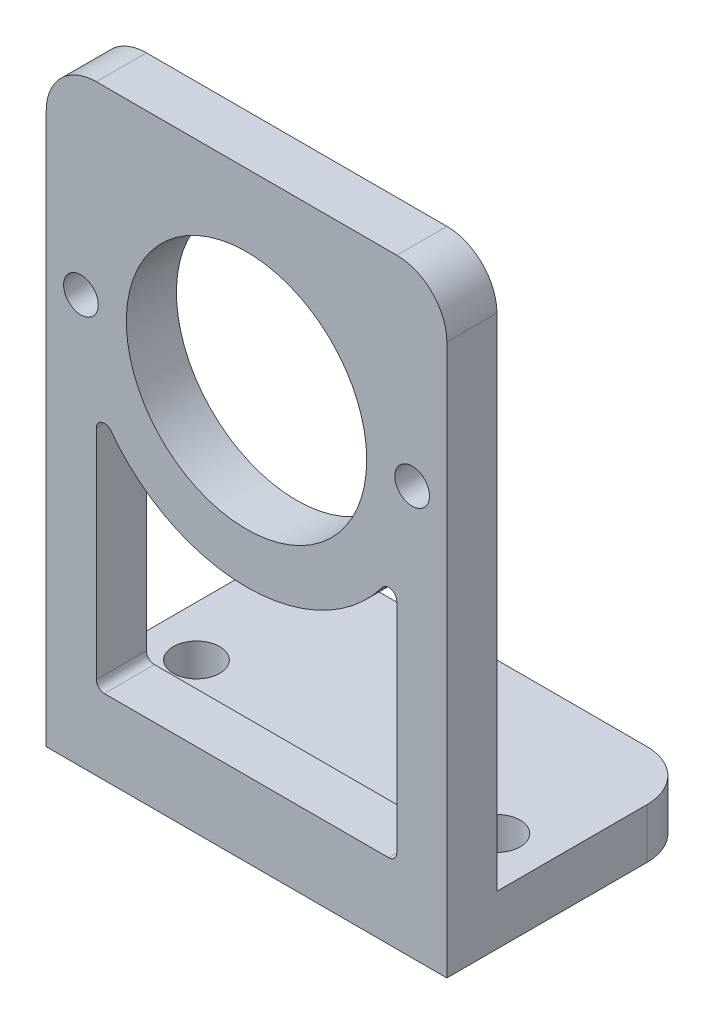
SolidWorks part; units mm, degrees
material "6061-T6 (SS)"
ref_plane "Front Plane" through (0, 0, 0) normal (0, 0, 1) x (1, 0, 0)
ref_plane "Top Plane" through (0, 0, 0) normal (0, 1, 0) x (1, 0, 0)
ref_plane "Right Plane" through (0, 0, 0) normal (1, 0, 0) x (0, 0, -1)
sketch "Sketch1" plane through (0, 0, 0) normal (1, 0, 0) x (0, 0, -1)
  line L0 (0, 38.1) -> (0, 0)
  line L1 (0, 0) -> (15.875, 0)
  line L2 (15.875, 0) -> (15.875, 3.175)
  line L3 (15.875, 3.175) -> (3.175, 3.175)
  line L4 (3.175, 3.175) -> (3.175, 38.1)
  line L5 (3.175, 38.1) -> (0, 38.1)
  dimension "D1" = 38.1
  dimension "D2" = 12.7
  dimension "D3" = 3.175
extrude "Boss-Extrude1" add sketch "Sketch1" along normal mid plane 25.4
sketch "Sketch2" plane through (0, 0, 0) normal (0, 0, 1) x (1, 0, 0)
  line L0 (12.7, 0) -> (-12.7, 0) construction
  circle A0 centre (0, 25.908) radius 7.62
  dimension "D2" = 15.24
  dimension "D1" = 25.908
extrude "Cut-Extrude1" cut sketch "Sketch2" against normal through all
fillet "Fillet1" radius 3.175 4 edges at (-12.7, 1.5875, -15.875) (12.7, 1.5875, -15.875) (-12.7, 38.1, -1.5875) (12.7, 38.1, -1.5875)
hole_wizard "#4 Clearance Hole1" positions "Sketch3" profile "Sketch4" hole size "#4" standard "ANSI Inch" end condition through all
sketch "Sketch3" plane through (0, 3.175, 0) normal (0, 1, 0) x (1, 0, 0)
  line L0 (-9.525, 6.35) -> (0, 0)
  line L1 (0, 0) -> (9.525, 6.35)
  line L3 (12.7, 3.175) -> (-12.7, 3.175) construction
  point P0 (-9.525, 6.35)
  point P2 (0, 12.7)
  point P4 (9.525, 6.35)
  dimension "D1" = 19.05
  dimension "D2" = 6.35
  dimension "D3" = 3.175
sketch "Sketch4" plane through (-9.525, 3.175, -6.35) normal (1, 0, 0) x (0, 0, 1)
  line L0 (0, 0) -> (0, 3.175)
  line L1 (0, 3.175) -> (1.4732, 3.175)
  line L2 (1.4732, 3.175) -> (1.4732, 0)
  line L5 (1.4732, 0) -> (0, 0)
  line L11 (0, -6.35) -> (0, 107.95) construction
  dimension "Thru Hole Dia." = 2.9464
  dimension "Thru Hole Depth" = 3.175
hole_wizard "M2 Clearance Hole1" positions "Sketch5" profile "Sketch6" hole size "M2" standard "ANSI Metric" end condition through all
sketch "Sketch5" plane through (32.8513, 6.6459, 0) normal (0, 0, 1) x (0, 1, 0)
  point P0 (19.2621, 22.3513)
  point P2 (19.2621, 43.3513)
sketch "Sketch6" plane through (10.5, 25.908, 0) normal (1, 0, 0) x (0, -1, 0)
  line L0 (0, 0) -> (0, 15.875)
  line L1 (0, 15.875) -> (1.1, 15.875)
  line L2 (1.1, 15.875) -> (1.1, 0)
  line L3 (1.1, 0) -> (0, 0)
  line L4 (0, -6.35) -> (0, 107.95) construction
  dimension "Thru Hole Dia." = 2.2
  dimension "Thru Hole Depth" = 15.875
sketch "Sketch7" plane through (0, 0, 0) normal (0, 0, 1) x (1, 0, 0)
  line L0 (-9.525, 20.828) -> (-9.525, 4.7625)
  line L1 (-9.525, 4.7625) -> (9.525, 4.7625)
  line L2 (9.525, 4.7625) -> (9.525, 20.828)
  line L3 (-12.7, 34.925) -> (-12.7, 0) construction
  line L4 (12.7, 34.925) -> (12.7, 0) construction
  line L5 (12.7, 3.175) -> (-12.7, 3.175) construction
  arc A0 (-9.525, 20.828) -> (9.525, 20.828) centre (0, 25.908) ccw
  circle A1 centre (0, 25.908) radius 7.62 construction
  dimension "D1" = 3.175
  dimension "D2" = 3.175
  dimension "D3" = 3.175
  dimension "D4" = 1.5875
extrude "Cut-Extrude2" cut sketch "Sketch7" against normal through all
fillet "Fillet2" radius 0.508 4 edges at (-9.525, 4.7625, -1.5875) (9.525, 4.7625, -1.5875) (9.525, 20.828, -1.5875) (-9.525, 20.828, -1.5875)
